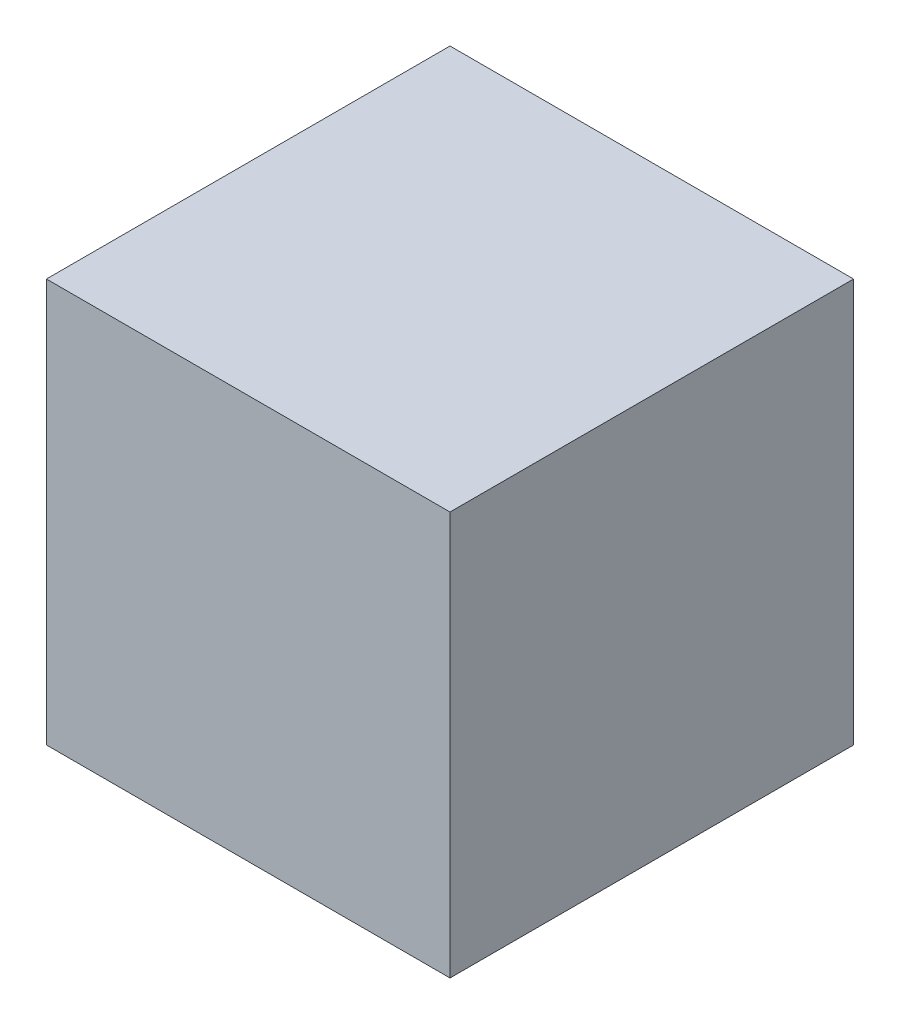
SolidWorks part; units mm, degrees
ref_plane "Front Plane" through (0, 0, 0) normal (0, 0, 1) x (1, 0, 0)
ref_plane "Top Plane" through (0, 0, 0) normal (0, 1, 0) x (1, 0, 0)
ref_plane "Right Plane" through (0, 0, 0) normal (1, 0, 0) x (0, 0, -1)
sketch "Sketch1" plane through (0, 0, 0) normal (0, 1, 0) x (1, 0, 0)
  line L1 (0, 0) -> (304.8, 0)
  line L2 (0, 0) -> (0, 304.8)
  line L3 (0, 304.8) -> (304.8, 304.8)
  line L4 (304.8, 0) -> (304.8, 304.8)
  dimension "D1" = 304.8
  dimension "D2" = 304.8
extrude "Extrude1" add sketch "Sketch1" along normal blind 304.8
